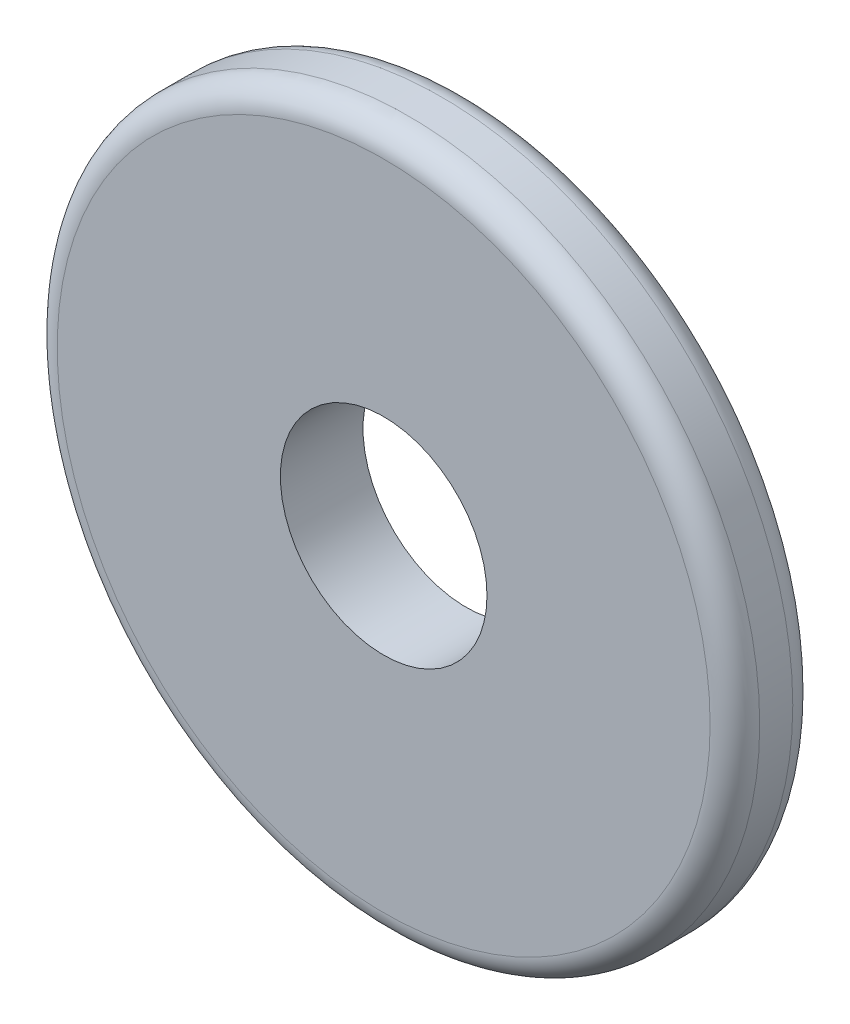
SolidWorks part; units mm, degrees
ref_plane "Front Plane" through (0, 0, 0) normal (0, 0, 1) x (1, 0, 0)
ref_plane "Top Plane" through (0, 0, 0) normal (0, 1, 0) x (1, 0, 0)
ref_plane "Right Plane" through (0, 0, 0) normal (1, 0, 0) x (0, 0, -1)
sketch "Sketch1" plane through (0, 0, 0) normal (0, 0, 1) x (1, 0, 0)
  circle A0 centre (0, 0) radius 12.5
  circle A1 centre (0, 0) radius 42.5
  dimension "D1" = 25
  dimension "D2" = 85
extrude "Boss-Extrude1" add sketch "Sketch1" along normal blind 10
fillet "Fillet1" radius 3 2 edges at (42.5, 0, 0) (42.5, 0, 10)
